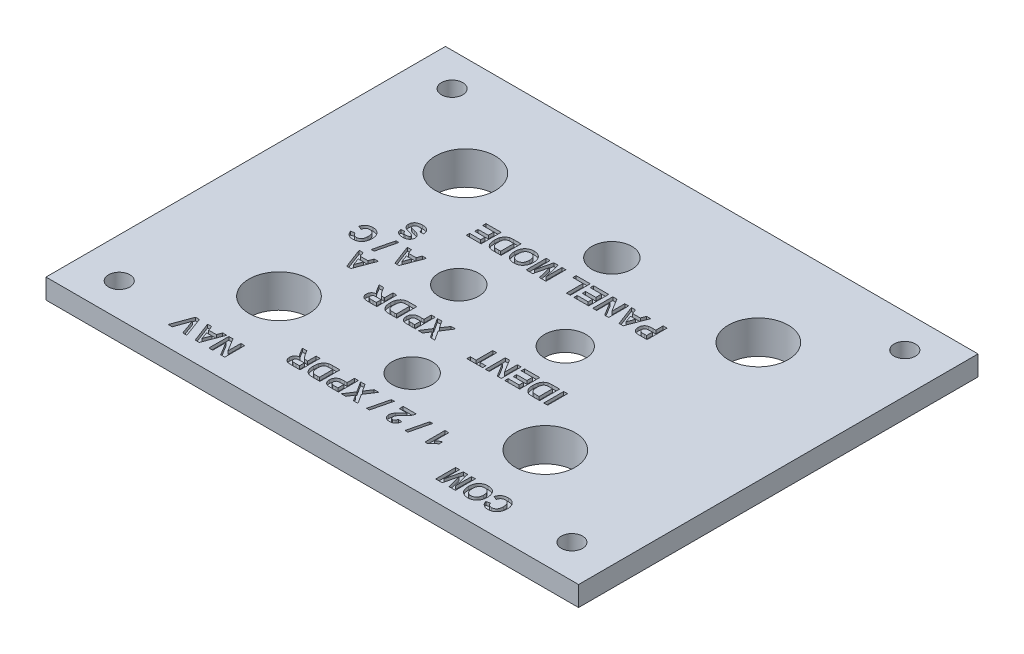
SolidWorks part; units mm, degrees
ref_plane "Спереди" through (0, 0, 0) normal (0, 0, 1) x (1, 0, 0)
ref_plane "Сверху" through (0, 0, 0) normal (0, 1, 0) x (1, 0, 0)
ref_plane "Справа" through (0, 0, 0) normal (1, 0, 0) x (0, 0, -1)
sketch "Sketch1" plane through (0, 0, 0) normal (0, 1, 0) x (1, 0, 0)
  line L1 (40, -30) -> (-40, -30)
  line L2 (40, -30) -> (40, 30)
  line L3 (40, 30) -> (-40, 30)
  line L4 (-40, -30) -> (-40, 30)
  line L5 (40, -30) -> (-40, 30) construction
  line L6 (40, 30) -> (-40, -30) construction
  point P0 (0, 0)
  dimension "D1" = 80
  dimension "D2" = 60
extrude "Boss-Extrude1" add sketch "Sketch1" along normal blind 3
sketch "Sketch2" plane through (0, 0, 0) normal (0, -1, 0) x (1, 0, 0)
  line L0 (40, -30) -> (-40, -30) construction
  line L1 (-36.7, 26.7) -> (36.7, 26.7)
  line L2 (-36.7, 26.7) -> (-36.7, -26.7)
  line L3 (-36.7, -26.7) -> (36.7, -26.7)
  line L4 (36.7, 26.7) -> (36.7, -26.7)
  line L5 (-36.7, 26.7) -> (36.7, -26.7) construction
  line L6 (-36.7, -26.7) -> (36.7, 26.7) construction
  line L7 (-40, -30) -> (-40, 30) construction
  point P0 (0, 0)
  dimension "D1" = 3.3
  dimension "D2" = 3.3
extrude "Boss-Extrude2" add sketch "Sketch2" along normal blind 2
chamfer "Chamfer1" distance 1 angle 30 4 edges at (0, -2, -26.7) (-36.7, -2, 0) (0, -2, 26.7) (36.7, -2, 0)
sketch "Sketch3" plane through (0, 3, 0) normal (0, 1, 0) x (1, 0, 0)
  line L0 (40, -15) -> (-40, -15) construction
  line L1 (40, -30) -> (40, 30) construction
  line L2 (-40, 30) -> (-40, -30) construction
  line L3 (-40, 15) -> (40, 15) construction
  line L4 (0, 15) -> (0, -15) construction
  line L5 (-40, -30) -> (40, -30) construction
  line L6 (40, -25) -> (-40, -25) construction
  line L7 (9, -6.5) -> (31, -6.5) construction
  line L8 (9, -6.5) -> (9, -23.5) construction
  line L9 (9, -23.5) -> (31, -23.5) construction
  line L10 (31, -6.5) -> (31, -23.5) construction
  line L11 (9, -6.5) -> (31, -23.5) construction
  line L12 (9, -23.5) -> (31, -6.5) construction
  line L13 (-31, -6.5) -> (-9, -6.5) construction
  line L14 (-31, -6.5) -> (-31, -23.5) construction
  line L15 (-31, -23.5) -> (-9, -23.5) construction
  line L16 (-9, -6.5) -> (-9, -23.5) construction
  line L17 (-31, -6.5) -> (-9, -23.5) construction
  line L18 (-31, -23.5) -> (-9, -6.5) construction
  line L19 (11, 23.5) -> (33, 23.5) construction
  line L20 (11, 23.5) -> (11, 6.5) construction
  line L21 (11, 6.5) -> (33, 6.5) construction
  line L22 (33, 23.5) -> (33, 6.5) construction
  line L23 (11, 23.5) -> (33, 6.5) construction
  line L24 (11, 6.5) -> (33, 23.5) construction
  line L25 (-11, 23.5) -> (-33, 23.5) construction
  line L26 (-11, 23.5) -> (-11, 6.5) construction
  line L27 (-11, 6.5) -> (-33, 6.5) construction
  line L28 (-33, 23.5) -> (-33, 6.5) construction
  line L29 (-11, 23.5) -> (-33, 6.5) construction
  line L30 (-11, 6.5) -> (-33, 23.5) construction
  line L31 (-40, 25) -> (40, 25) construction
  line L32 (40, 30) -> (-40, 30) construction
  line L33 (34, 25) -> (34, -25) construction
  line L34 (-34, -25) -> (-34, 25) construction
  line L35 (-8, 0) -> (8, 0) construction
  circle A0 centre (22, 15) radius 4.5
  circle A1 centre (-22, 15) radius 4.5
  circle A2 centre (-20, -15) radius 4.5
  circle A3 centre (20, -15) radius 4.5
  circle A4 centre (0, 15) radius 3
  circle A5 centre (0, -15) radius 3
  circle A6 centre (-34, -25) radius 1.6
  circle A7 centre (34, -25) radius 1.6
  circle A8 centre (34, 25) radius 1.6
  circle A9 centre (-34, 25) radius 1.6
  circle A10 centre (8, 0) radius 3.1
  circle A11 centre (-8, 0) radius 3
  point P55 (0, 0)
  point P56 (0, 0)
  dimension "D1" = 9
  dimension "D2" = 22
  dimension "D9" = 6
  dimension "D13" = 3.2
  dimension "D17" = 6.2
  dimension "D3" = 40
  dimension "D4" = 20
  dimension "D5" = 15
  dimension "D6" = 44
  dimension "D7" = 22
  dimension "D8" = 17
  dimension "D10" = 15
  dimension "D11" = 5
  dimension "D12" = 5
  dimension "D14" = 50
  dimension "D15" = 68
  dimension "D16" = 34
  dimension "D18" = 16
extrude "Cut-Extrude1" cut sketch "Sketch3" against normal through all
sketch "Sketch5" plane through (0, 3, 0) normal (0, 1, 0) x (1, 0, 0)
  line L0 (40, -24) -> (-40, -24) construction
  line L1 (40, -30) -> (40, 30) construction
  line L2 (-40, 30) -> (-40, -30) construction
  line L3 (40, 10) -> (-40, 10) construction
  line L4 (40, -6) -> (-40, -6) construction
  line L5 (-40, -30) -> (40, -30) construction
  line L6 (40, -20) -> (-40, -20) construction
  line L7 (40, -3) -> (-40, -3) construction
  line L8 (40, 1) -> (-40, 1) construction
  line L9 (40, 5) -> (-40, 5) construction
  line L10 (40, 30) -> (-40, 30) construction
  text T0 "<b>             COM                           NAV</b>" font "Arial" height 3
  text T1 "<b>1 / 2 / XPDR</b>" font "Arial" height 3
  text T2 "<b>                      IDENT    XPDR</b>" font "Arial" height 3
  text T3 "<b>                                A</b>" font "Arial" height 3
  text T4 "<b>                                A / C</b>" font "Arial" height 3
  text T5 "<b>                                S</b>" font "Arial" height 3
  text T6 "<b>PANEL MODE</b>" font "Arial" height 3
  dimension "D1" = 6
  dimension "D2" = 10
  dimension "D3" = 24
  dimension "D4" = 4
  dimension "D5" = 4
  dimension "D6" = 20
  dimension "D7" = 27
extrude "Cut-Extrude2" cut sketch "Sketch5" against normal blind 0.5
sketch "Sketch6" plane through (0, -2, 0) normal (0, -1, 0) x (1, 0, 0)
  circle A0 centre (8, 0) radius 7.5
  dimension "D1" = 15
extrude "Cut-Extrude3" cut sketch "Sketch6" against normal blind 2
